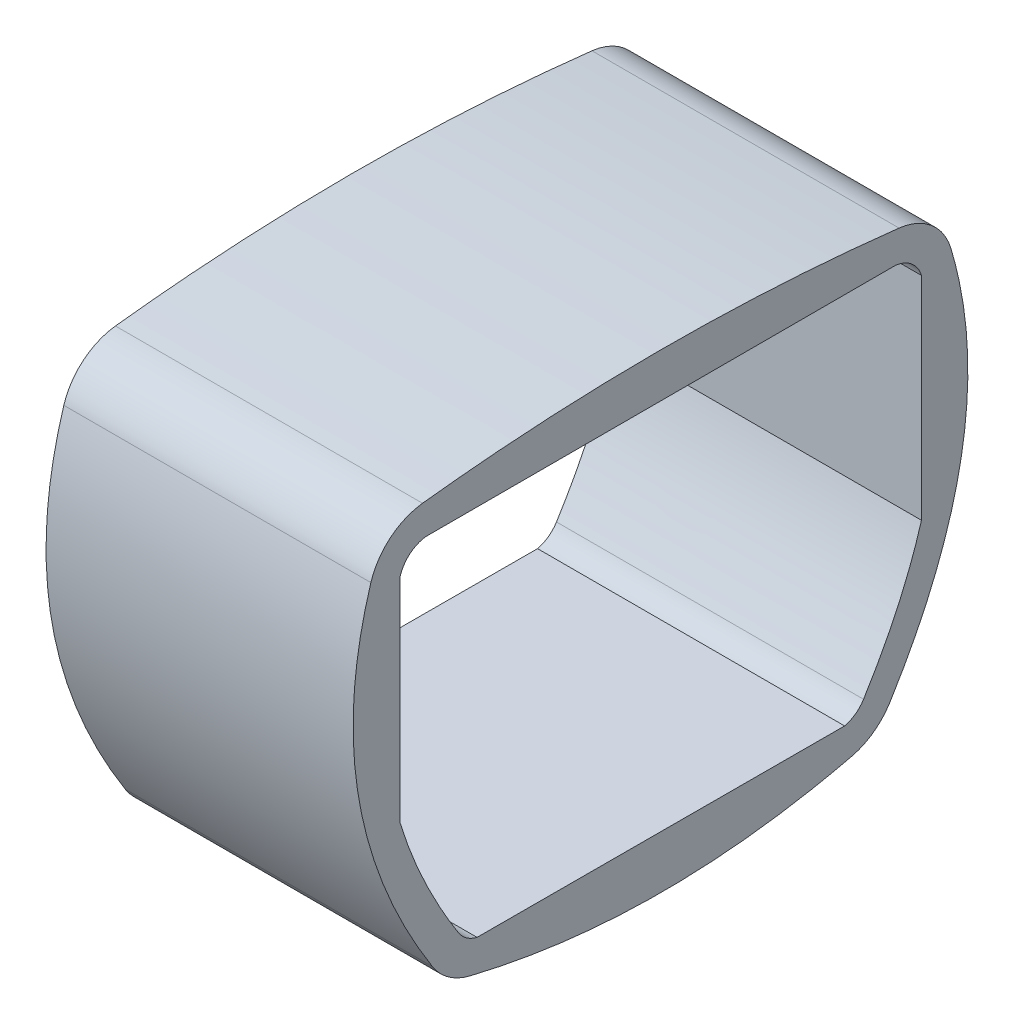
SolidWorks part; units mm, degrees
ref_plane "Front Plane" through (0, 0, 0) normal (0, 0, 1) x (1, 0, 0)
ref_plane "Top Plane" through (0, 0, 0) normal (0, 1, 0) x (1, 0, 0)
ref_plane "Right Plane" through (0, 0, 0) normal (1, 0, 0) x (0, 0, -1)
sketch "Sketch7" plane through (0, 0, 0) normal (0, 0, 1) x (1, 0, 0)
  line L0 (-53.1389, 136.7433) -> (-53.1389, -30.8967)
  line L2 (73.8611, -30.8967) -> (73.8611, 136.7433)
  spline S0 degree 2 poles (-53.1389, -30.8967) (10.3808, -42.9091) (73.8611, -30.8967) knots 0 0 0 1 1 1
  spline S1 degree 2 poles (-53.1389, 136.7433) (10.3648, 141.9324) (73.8611, 136.7433) knots 0 0 0 1 1 1
  dimension "D1" = 127
  dimension "D2" = 167.64
sketch "Sketch8" plane through (0, 0, 0) normal (1, 0, 0) x (0, 0, -1)
  spline S0 degree 2 poles (-89.5173, -36.7354) (-0.6341, -60.9752) (88.2824, -37.028) knots 0 0 0 1 1 1
  spline S1 degree 2 poles (-114.9014, 137.8778) (-0.596, 153.1681) (113.6986, 137.8778) knots 0 0 0 1 1 1
  spline S2 degree 2 poles (113.6986, 137.8778) (148.206, 51.8147) (88.2824, -37.028) knots 0 0 0 1 1 1
  spline S3 degree 2 poles (-114.9014, 137.8778) (-150.3079, 52.1414) (-89.5173, -36.7354) knots 0 0 0 1 1 1
  dimension "D1" = 177.8
  dimension "D2" = 228.6
extrude "Boss-Extrude8" add sketch "Sketch8" along normal blind 127
fillet "Fillet4" radius 25.4 3 edges at (63.5, 137.8778, 114.9014)
fillet "Fillet5" radius 25.4 3 edges at (63.5, -36.7354, 89.5173)
fillet "Fillet6" radius 25.4 3 edges at (63.5, -37.028, -88.2824)
fillet "Fillet7" radius 25.4 3 edges at (63.5, 137.8778, -113.6986)
sketch "Sketch11" plane through (127, 0, 0) normal (1, 0, 0) x (0, 0, -1)
  line L0 (-97.7845, 127.2129) -> (96.4046, 127.2335)
  line L1 (107.121, 118.2463) -> (107.121, 30.5559)
  line L2 (-108.4626, 118.3439) -> (-108.4626, 29.8571)
  line L3 (-76.6906, -26.9275) -> (75.3429, -27.2138)
  arc A8 (107.121, 118.2463) -> (96.4046, 127.2335) centre (94.9507, 114.617) ccw
  arc A9 (-97.7845, 127.2129) -> (-108.4626, 118.3439) centre (-96.328, 114.5967) ccw
  arc A10 (-84.4264, -21.3774) -> (-76.6906, -26.9275) centre (-73.6949, -14.5858) ccw
  arc A11 (75.3429, -27.2138) -> (83.1705, -21.5781) centre (72.392, -14.8613) ccw
  arc A12 (107.121, 118.2463) -> (96.4046, 127.2335) centre (94.9507, 114.617) ccw
  arc A13 (-97.7845, 127.2129) -> (-108.4626, 118.3439) centre (-96.328, 114.5967) ccw
  arc A14 (-84.4264, -21.3774) -> (-76.6906, -26.9275) centre (-73.6949, -14.5858) ccw
  arc A15 (75.3429, -27.2138) -> (83.1705, -21.5781) centre (72.392, -14.8613) ccw
  spline S0 degree 3 poles (3016.3397, -2430.2064) (-1176.0345, -323.8831) (-87.3184, -348.1827) (95.101, -0.3263) (97.6974, 5.1425) (102.3834, 16.2845) (104.4731, 21.9577) (108.0738, 33.5376) (109.5849, 39.4443) (111.0557, 46.9962) (111.3293, 48.5175) (111.8297, 51.5571) (112.5114, 56.117) (112.9856, 60.6783) (113.6548, 69.8028) (113.7286, 75.8884) (113.2726, 85.0206) (112.9029, 89.5877) (112.3194, 94.1562) (111.8829, 97.2023) (111.6404, 98.7272) (39.5826, 511.4478) (-1700.6375, 534.9278) (3214.6943, 2105.0686) knots -7.834602 -7.834602 -7.834602 -7.834602 0.125 0.125 0.25 0.25 0.375 0.375 0.5 0.5 0.53125 0.53125 0.5625 0.625 0.625 0.75 0.75 0.8125 0.84375 0.84375 0.875 0.875 9.325801 9.325801 9.325801 9.325801 only from (83.1705, -21.5781) to (107.121, 118.2463)
  spline S1 degree 3 poles (946.2167, -399.8496) (314.8412, 310.7085) (-316.459, 310.0101) (-947.684, -399.7252) knots -4.375923 -4.375923 -4.375923 -4.375923 5.376949 5.376949 5.376949 5.376949 only from (96.4046, 127.2335) to (-97.7845, 127.2129)
  spline S2 degree 3 poles (-1852.6531, 1961.4254) (3023.3853, 758.5654) (-84.2318, 626.9413) (-115.1754, 79.4308) (-115.2514, 76.3783) (-115.2077, 70.2473) (-115.0871, 67.1604) (-114.4385, 57.9836) (-112.8134, 45.9042) (-109.8009, 34.1102) (-107.0653, 25.3626) (-106.0739, 22.4627) (-103.9395, 16.6957) (-102.8033, 13.8468) (-99.2036, 5.3962) (-96.5496, -0.1099) (75.0181, -322.3244) (999.846, -259.4001) (-2907.575, -2623.3119) knots -10.94552 -10.94552 -10.94552 -10.94552 0.25 0.25 0.3125 0.3125 0.375 0.375 0.5 0.625 0.625 0.6875 0.6875 0.75 0.75 0.875 0.875 8.214175 8.214175 8.214175 8.214175 only from (-108.4626, 118.3439) to (-84.4264, -21.3774)
  spline S3 degree 3 poles (-716.0116, 742.0101) (-492.0584, 278.3662) (-257.5492, -35.51) (5.3956, -36.2455) (14.9614, -35.9833) (24.558, -35.2822) (30.9627, -34.7168) (34.1707, -34.3846) (319.3827, -0.5218) (538.2967, 403.2397) (778.1428, 684.1723) knots -4.540028 -4.540028 -4.540028 -4.540028 0.5 0.5 0.625 0.6875 0.6875 0.75 0.75 6.26429 6.26429 6.26429 6.26429 only from (-76.6906, -26.9275) to (75.3429, -27.2138)
  spline S4 degree 3 poles (83.1705, -21.5781) (86.4154, -16.371) (89.4601, -11.083) (95.101, -0.3263) (97.6974, 5.1425) (102.3834, 16.2845) (104.4731, 21.9577) (106.5635, 28.6807) (106.8461, 29.6168) (107.121, 30.5559) knots 0 0 0 0 0.125 0.125 0.25 0.25 0.375 0.375 0.395143 0.395143 0.395143 0.395143
  spline S6 degree 3 poles (-108.4626, 29.8571) (-108.3034, 29.3304) (-108.1416, 28.8042) (-107.0653, 25.3626) (-106.0739, 22.4627) (-103.9395, 16.6957) (-102.8033, 13.8468) (-99.2036, 5.3962) (-96.5496, -0.1099) (-90.8032, -10.9019) (-87.7107, -16.1878) (-84.4264, -21.3774) knots 0.613732 0.613732 0.613732 0.613732 0.625 0.625 0.6875 0.6875 0.75 0.75 0.875 0.875 1 1 1 1
  dimension "D1" = 12.7
extrude "Cut-Extrude3" cut sketch "Sketch11" against normal blind 127
